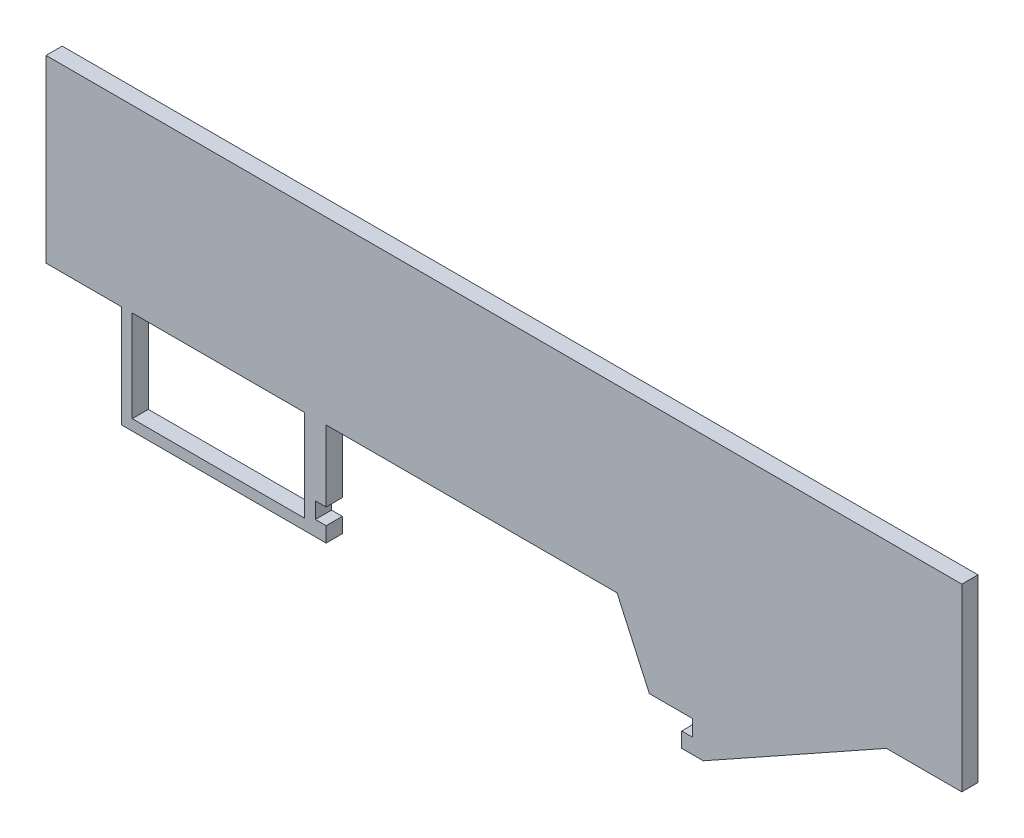
SolidWorks part; units mm, degrees
ref_plane "Front Plane" through (0, 0, 0) normal (0, 0, 1) x (1, 0, 0)
ref_plane "Top Plane" through (0, 0, 0) normal (0, 1, 0) x (1, 0, 0)
ref_plane "Right Plane" through (0, 0, 0) normal (1, 0, 0) x (0, 0, -1)
sketch "Sketch1" plane through (0, 0, 0) normal (0, 0, 1) x (1, 0, 0)
  line L1 (-42.5, 23.3) -> (42.5, 23.3)
  line L2 (-42.5, 23.3) -> (-42.5, 6.6)
  line L4 (42.5, 23.3) -> (42.5, 6.6)
  line L15 (42.5, 6.6) -> (-42.5, 6.6) construction
  line L16 (0, 23.3) -> (0, 0) construction
  line L17 (42.5, 6.6) -> (35.5, 6.6)
  line L18 (35.5, 6.6) -> (18.5, -2.9)
  line L19 (18.5, -2.9) -> (16.5, -2.9)
  line L20 (16.5, -2.9) -> (16.5, -1.5)
  line L21 (16.5, -1.5) -> (17.5, -1.5)
  line L22 (17.5, -1.5) -> (17.5, 0)
  line L23 (17.5, 0) -> (13.5, 0)
  line L24 (13.5, 0) -> (10.5, 6.6)
  line L25 (10.5, 6.6) -> (-16.5, 6.6)
  line L26 (-16.5, 6.6) -> (-16.5, 0)
  line L27 (-16.5, 0) -> (-17.5, 0)
  line L28 (-17.5, 0) -> (-17.5, -1.5)
  line L29 (-17.5, -1.5) -> (-16.5, -1.5)
  line L30 (-16.5, -1.5) -> (-16.5, -2.9)
  line L31 (-16.5, -2.9) -> (-35.5, -2.9)
  line L32 (-35.5, -2.9) -> (-35.5, 6.6)
  line L33 (-35.5, 6.6) -> (-42.5, 6.6)
  line L34 (-34.5, 6.6) -> (-34.5, -1.9)
  line L35 (-34.5, -1.9) -> (-18.5, -1.9)
  line L36 (-18.5, -1.9) -> (-18.5, 6.6)
  line L37 (-18.5, 6.6) -> (-34.5, 6.6)
  line L38 (-17.5, 0) -> (17.5, 0) construction
  dimension "D1" = 85
  dimension "D2" = 16.7
  dimension "D3" = 9.5
  dimension "D4" = 1.5
  dimension "D5" = 1.4
  dimension "D6" = 35
  dimension "D7" = 1
  dimension "D8" = 1
  dimension "D9" = 4
  dimension "D10" = 7
  dimension "D11" = 7
  dimension "D12" = 1
  dimension "D13" = 1
  dimension "D14" = 1
  dimension "D15" = 32
  dimension "D16" = 2
extrude "Boss-Extrude1" add sketch "Sketch1" along normal blind 1.5
ref_plane "Plane1" through (0, 0, 0) normal (1, 0, 0) x (0, 0, -1)
